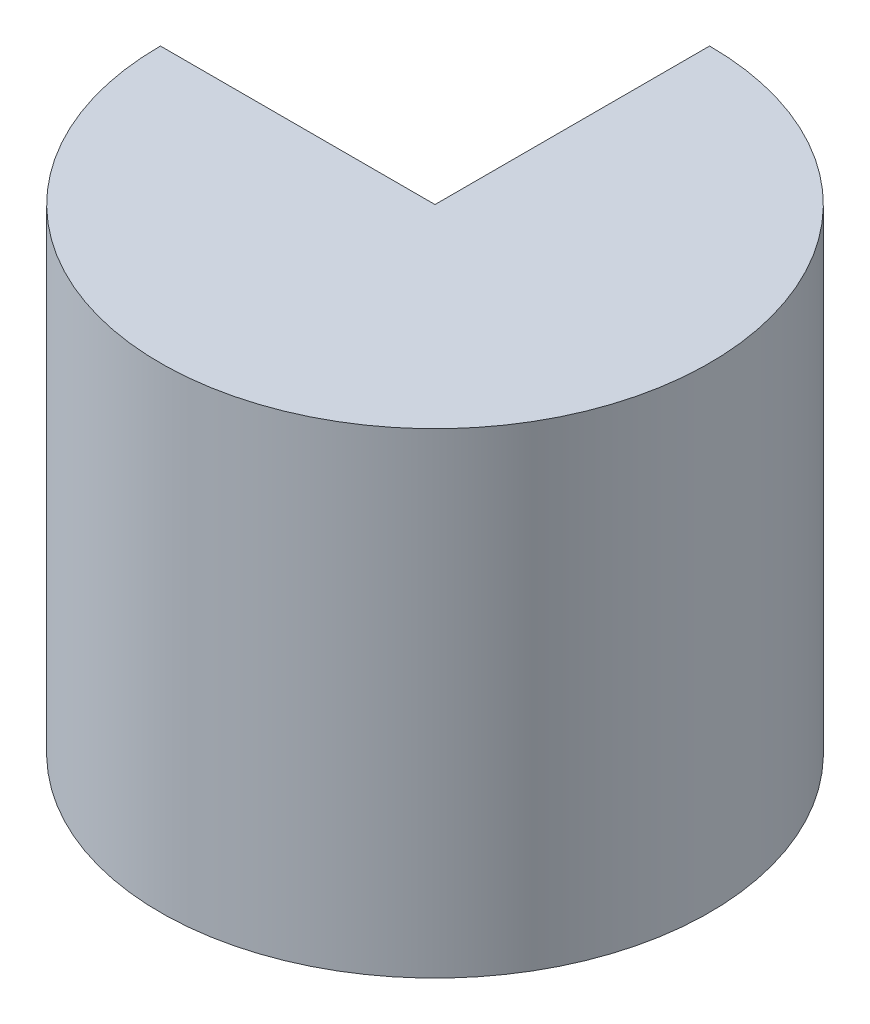
SolidWorks part; units mm, degrees
ref_plane "Front Plane" through (0, 0, 0) normal (0, 0, 1) x (1, 0, 0)
ref_plane "Top Plane" through (0, 0, 0) normal (0, 1, 0) x (1, 0, 0)
ref_plane "Right Plane" through (0, 0, 0) normal (1, 0, 0) x (0, 0, -1)
sketch "Sketch1" plane through (0, 0, 0) normal (1, 0, 0) x (0, 0, -1)
  line L5 (25.654, 45.0234) -> (25.654, 0.5734)
  line L12 (0, 45.0234) -> (0, 0) construction
  line L20 (25.654, 45.0234) -> (3.175, 45.0234)
  line L21 (25.654, 0.5734) -> (3.175, 0.5734)
  line L22 (3.175, 45.0234) -> (0, 45.0234)
  line L23 (3.175, 0.5734) -> (0, 0.5734)
  line L24 (0, 45.0234) -> (0, 0.5734)
  dimension "D1" = 44.45
revolve "Revolve2" add sketch "Sketch1" angle 270 about L12
